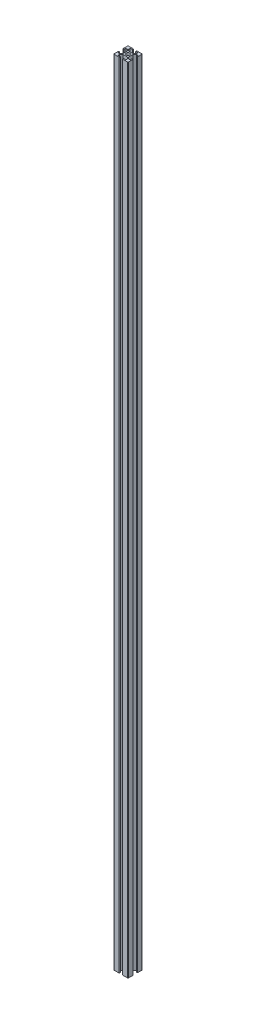
SolidWorks part; units mm, degrees
ref_plane "前视基准面" through (0, 0, 0) normal (0, 0, 1) x (1, 0, 0)
ref_plane "上视基准面" through (0, 0, 0) normal (0, 1, 0) x (1, 0, 0)
ref_plane "右视基准面" through (0, 0, 0) normal (1, 0, 0) x (0, 0, -1)
sketch "草图1" plane through (0, 0, 0) normal (0, 0, 1) x (1, 0, 0)
  line L0 (0, 1108) -> (0, 0)
other "铝型材 20 X 20 X 2(1)"
ref_plane "基准面4" through (0, 1108, 0) normal (0, -1, 0) x (1, 0, 0)
sketch "草图11" plane through (0, 1108, 0) normal (0, -1, 0) x (1, 0, 0)
  line L175 (-10, 9) -> (-10, 3.25)
  line L176 (-9, -10) -> (-2.25, -10)
  line L177 (-10, -3.25) -> (-10, -9)
  line L178 (-9, 10) -> (-2.25, 10)
  line L179 (-2.25, -8.5) -> (-2.25, -10)
  line L180 (-2.25, 8.5) -> (-2.25, 10)
  line L181 (-8.5, 3.25) -> (-10, 3.25)
  line L182 (-8.5, 5.5) -> (-8.5, 3.25)
  line L183 (-10, 0) -> (10, 0) construction
  line L184 (-3.1515, -4) -> (3.1515, -4)
  line L185 (-3.1515, 4) -> (3.1515, 4)
  line L186 (-8.5, 5.5) -> (-6.3485, 5.5)
  line L187 (0, -10) -> (0, 10) construction
  line L188 (-4, -3.1515) -> (-4, 3.1515)
  line L189 (-8.5, -3.25) -> (-10, -3.25)
  line L190 (-8.5, -5.5) -> (-8.5, -3.25)
  line L191 (-8.5, -5.5) -> (-6.3485, -5.5)
  line L192 (-4, 3.1515) -> (-6.3485, 5.5)
  line L193 (-4, -3.1515) -> (-6.3485, -5.5)
  line L194 (-5.5, -8.5) -> (-2.25, -8.5)
  line L195 (-5.5, -8.5) -> (-5.5, -6.3485)
  line L196 (-3.1515, -4) -> (-5.5, -6.3485)
  line L197 (-5.5, 8.5) -> (-2.25, 8.5)
  line L198 (-5.5, 8.5) -> (-5.5, 6.3485)
  line L199 (-3.1515, 4) -> (-5.5, 6.3485)
  line L200 (10, 9) -> (10, 3.25)
  line L201 (9, -10) -> (2.25, -10)
  line L202 (10, -3.25) -> (10, -9)
  line L203 (9, 10) -> (2.25, 10)
  line L204 (2.25, -8.5) -> (2.25, -10)
  line L205 (2.25, 8.5) -> (2.25, 10)
  line L206 (8.5, 3.25) -> (10, 3.25)
  line L207 (8.5, 5.5) -> (8.5, 3.25)
  line L208 (8.5, 5.5) -> (6.3485, 5.5)
  line L209 (4, -3.1515) -> (4, 3.1515)
  line L210 (8.5, -3.25) -> (10, -3.25)
  line L211 (8.5, -5.5) -> (8.5, -3.25)
  line L212 (8.5, -5.5) -> (6.3485, -5.5)
  line L213 (4, 3.1515) -> (6.3485, 5.5)
  line L214 (4, -3.1515) -> (6.3485, -5.5)
  line L215 (5.5, -8.5) -> (2.25, -8.5)
  line L216 (5.5, -8.5) -> (5.5, -6.3485)
  line L217 (3.1515, -4) -> (5.5, -6.3485)
  line L218 (5.5, 8.5) -> (2.25, 8.5)
  line L219 (5.5, 8.5) -> (5.5, 6.3485)
  line L220 (3.1515, 4) -> (5.5, 6.3485)
  arc A28 (-10, -9) -> (-9, -10) centre (-9, -9) ccw
  arc A29 (-9, 10) -> (-10, 9) centre (-9, 9) ccw
  circle A30 centre (0, 0) radius 2.5
  arc A31 (9, -10) -> (10, -9) centre (9, -9) ccw
  arc A32 (10, 9) -> (9, 10) centre (9, 9) ccw
  point P0 (0, 0)
